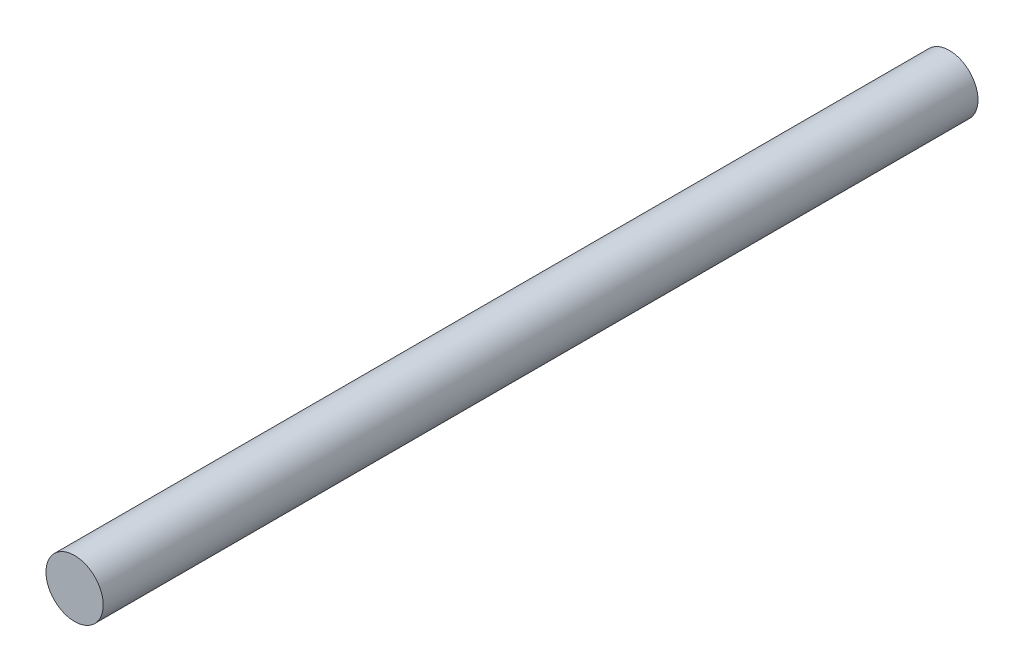
SolidWorks part; units mm, degrees
ref_plane "Front Plane" through (0, 0, 0) normal (0, 0, 1) x (1, 0, 0)
ref_plane "Top Plane" through (0, 0, 0) normal (0, 1, 0) x (1, 0, 0)
ref_plane "Right Plane" through (0, 0, 0) normal (1, 0, 0) x (0, 0, -1)
sketch "Sketch1" plane through (0, 0, 0) normal (0, 0, 1) x (1, 0, 0)
  circle A0 centre (0, 0) radius 3.175
  dimension "D1" = 6.35
extrude "Boss-Extrude1" add sketch "Sketch1" along normal mid plane 97
